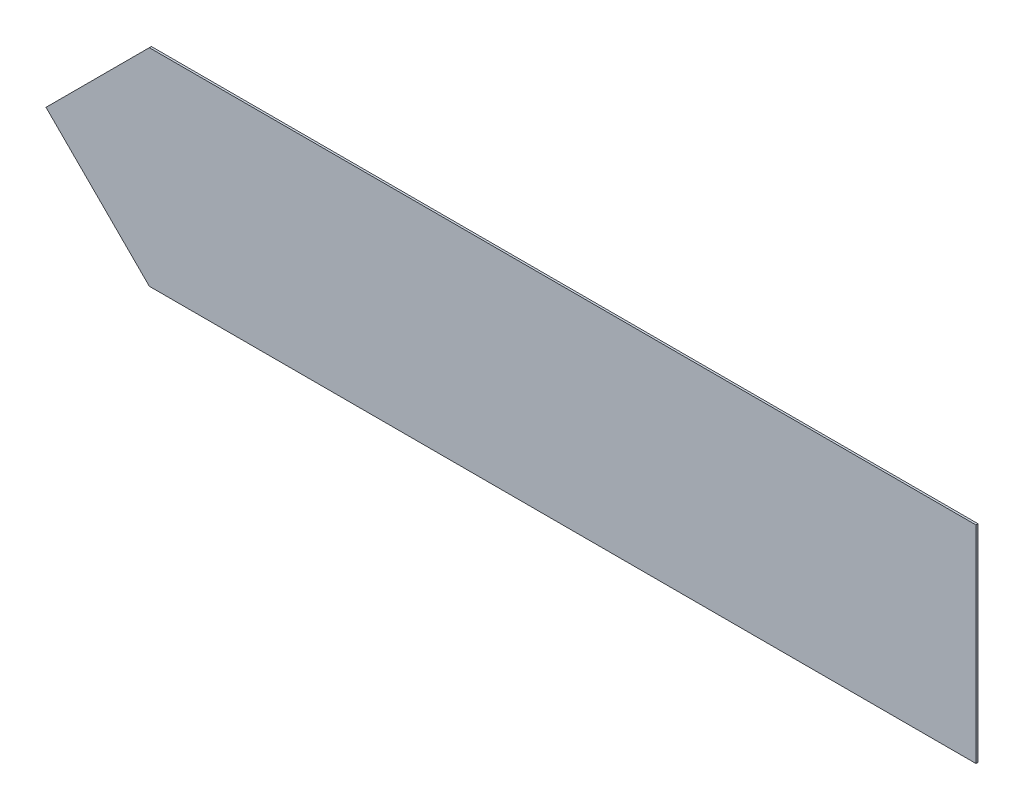
SolidWorks part; units mm, degrees
material "1060 Alloy"
ref_plane "Front Plane" through (0, 0, 0) normal (0, 0, 1) x (1, 0, 0)
ref_plane "Top Plane" through (0, 0, 0) normal (0, 1, 0) x (1, 0, 0)
ref_plane "Right Plane" through (0, 0, 0) normal (1, 0, 0) x (0, 0, -1)
sketch "Sketch1" plane through (0, 0, 0) normal (0, 0, 1) x (1, 0, 0)
  line L0 (0, 0) -> (12.7, 12.7)
  line L1 (12.7, 12.7) -> (114.3, 12.7)
  line L2 (114.3, 12.7) -> (114.3, -12.7)
  line L3 (114.3, 0) -> (0, 0) construction
  line L4 (12.7, -12.7) -> (114.3, -12.7)
  line L5 (0, 0) -> (12.7, -12.7)
  dimension "D1" = 12.7
  dimension "D2" = 101.6
  dimension "D3" = 12.7
extrude "Boss-Extrude1" add sketch "Sketch1" along normal blind 0.254
